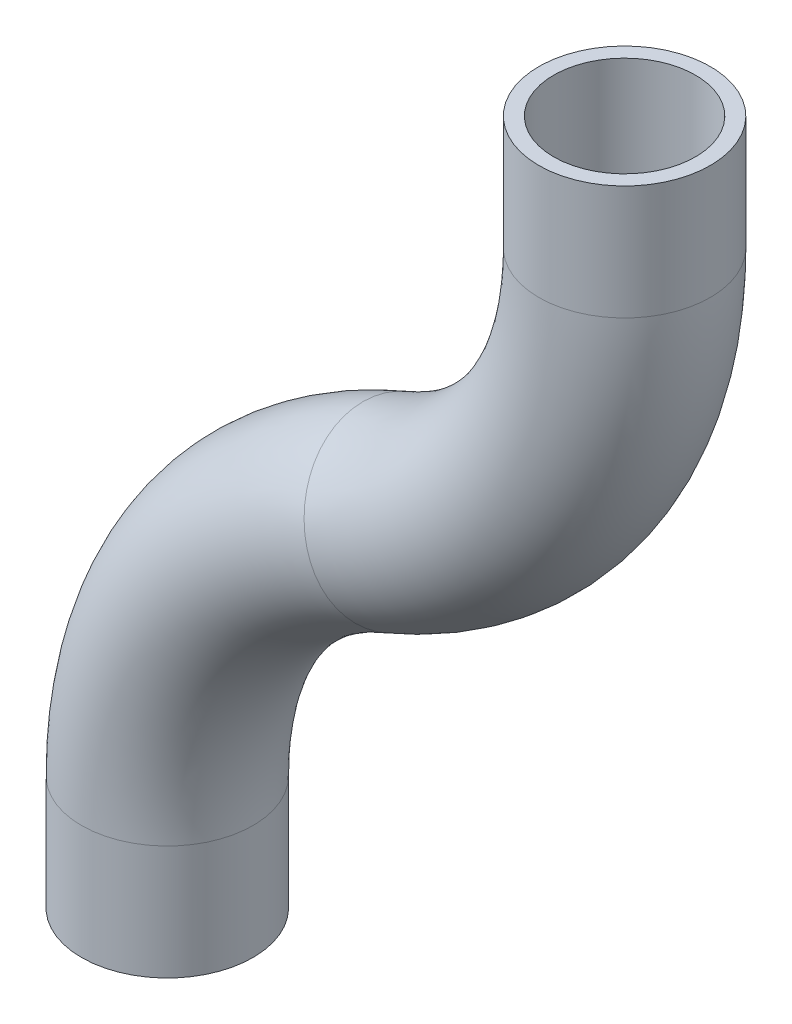
SolidWorks part; units mm, degrees
material "6061 Alloy"
ref_plane "Front Plane" through (0, 0, 0) normal (0, 0, 1) x (1, 0, 0)
ref_plane "Top Plane" through (0, 0, 0) normal (0, 1, 0) x (1, 0, 0)
ref_plane "Right Plane" through (0, 0, 0) normal (1, 0, 0) x (0, 0, -1)
sketch "Sketch1" plane through (0, 0, 0) normal (0, 1, 0) x (1, 0, 0)
  circle A0 centre (0, 0) radius 7.874
  circle A1 centre (0, 0) radius 9.525
  dimension "D1" = 19.05
  dimension "D2" = 1.651
sketch "Sketch2" plane through (0, 0, 0) normal (0, 0, 1) x (1, 0, 0)
  line L0 (0, 0) -> (0, 12.7)
  line L1 (50.8, 88.9) -> (50.8, 101.6)
  arc A0 (0, 12.7) -> (25.4, 50.8) centre (41.275, 12.7) cw
  arc A1 (25.4, 50.8) -> (50.8, 88.9) centre (9.525, 88.9) ccw
  dimension "D2" = 101.6
  dimension "D3" = 12.7
  dimension "D1" = 50.8
sweep "Sweep1" add profiles "Sketch1" path "Sketch2"
ref_plane "Plane1" through (50.8, 0, 0) normal (1, 0, 0) x (0, 0, -1)
